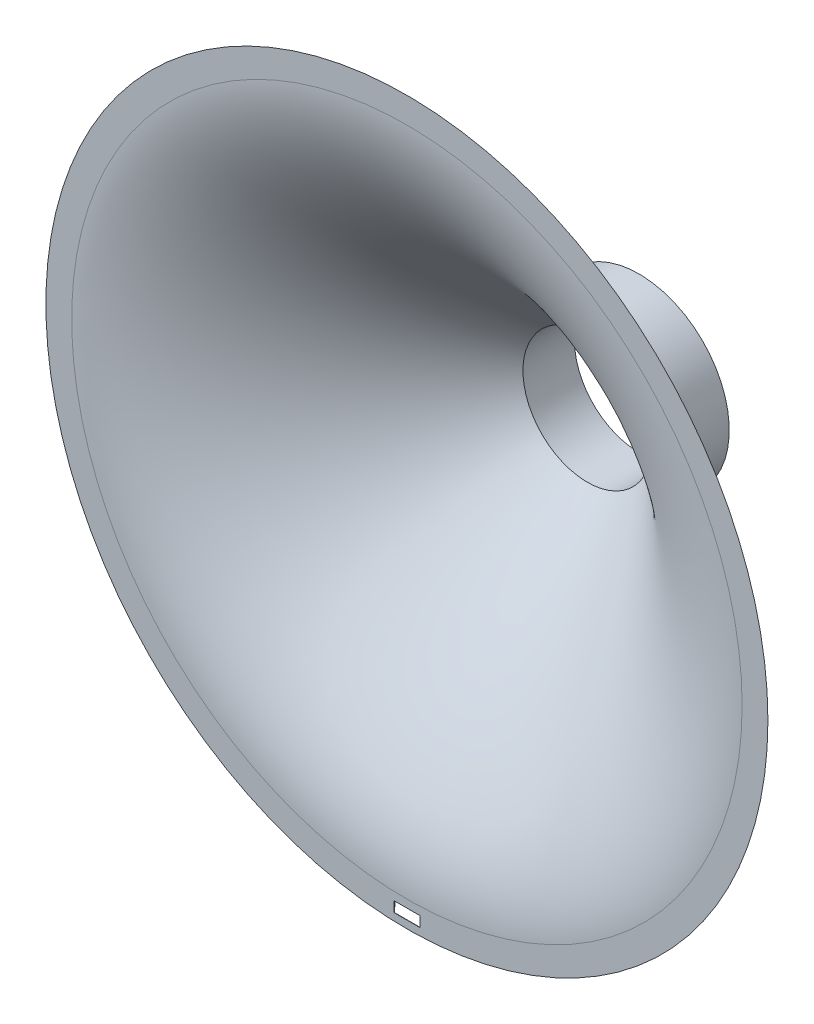
SolidWorks part; units mm, degrees
ref_plane "Front Plane" through (0, 0, 0) normal (0, 0, 1) x (1, 0, 0)
ref_plane "Top Plane" through (0, 0, 0) normal (0, 1, 0) x (1, 0, 0)
ref_plane "Right Plane" through (0, 0, 0) normal (1, 0, 0) x (0, 0, -1)
other "Bounding Box"
ref_plane "Default Plane" through (-70, -70, -45) normal (0, 1, 0) x (1, 0, 0)
sketch "Sketch1" plane through (0, 0, 0) normal (1, 0, 0) x (0, 0, -1)
  line L0 (0, 65) -> (0, 47.5) construction
  line L1 (0, 47.5) -> (22.6256, 24.8744) construction
  line L2 (22.6256, 24.8744) -> (35, 12.5) construction
  line L3 (0, 0) -> (0, 16.4687) construction
  line L4 (0, 70) -> (0, 52.5) construction
  line L5 (0, 52.5) -> (22.6256, 29.8744) construction
  line L6 (22.6256, 29.8744) -> (35, 17.5) construction
  line L7 (0, 65) -> (0, 70)
  line L8 (35, 17.5) -> (35, 12.5)
  line L9 (0, 0) -> (22.8545, 0) construction
  spline S0 degree 3 poles (0, 65) (0, 47.5) (22.6256, 24.8744) (35, 12.5) knots 0 0 0 0 1 1 1 1
  spline S1 degree 3 poles (0, 70) (0, 52.5) (22.6256, 29.8744) (35, 17.5) knots 0 0 0 0 1 1 1 1
  dimension "D1" = 52.5
  dimension "D2" = 35
  dimension "D3" = 65
  dimension "D4" = 5
  dimension "D5" = 135
revolve "Revolve1" add sketch "Sketch1" angle 360 about L9
sketch "Sketch2" plane through (0, 0, 0) normal (0, 0, 1) x (1, 0, 0)
  line L4 (0, -65) -> (0, -70) construction
  line L5 (-2.5, -68.5) -> (2.5, -68.5)
  line L6 (-2.5, -68.5) -> (-2.5, -66.5)
  line L7 (-2.5, -66.5) -> (2.5, -66.5)
  line L8 (2.5, -68.5) -> (2.5, -66.5)
  line L9 (-2.5, -68.5) -> (2.5, -66.5) construction
  line L10 (-2.5, -66.5) -> (2.5, -68.5) construction
  circle A1 centre (0, 0) radius 65 construction
  circle A2 centre (0, 0) radius 70 construction
  point P0 (0, -67.5)
  point P13 (0, -67.5)
  dimension "D1" = 2
  dimension "D2" = 5
extrude "Cut-Extrude3" cut sketch "Sketch2" against normal blind 10
sketch "Sketch3" plane through (0, 0, -35) normal (0, 0, -1) x (-1, 0, 0)
  circle A0 centre (0, 0) radius 17.5
  circle A1 centre (0, 0) radius 12.5
  circle A2 centre (0, 0) radius 12.5 construction
  circle A3 centre (0, 0) radius 17.5 construction
extrude "Boss-Extrude1" add sketch "Sketch3" along normal blind 10
